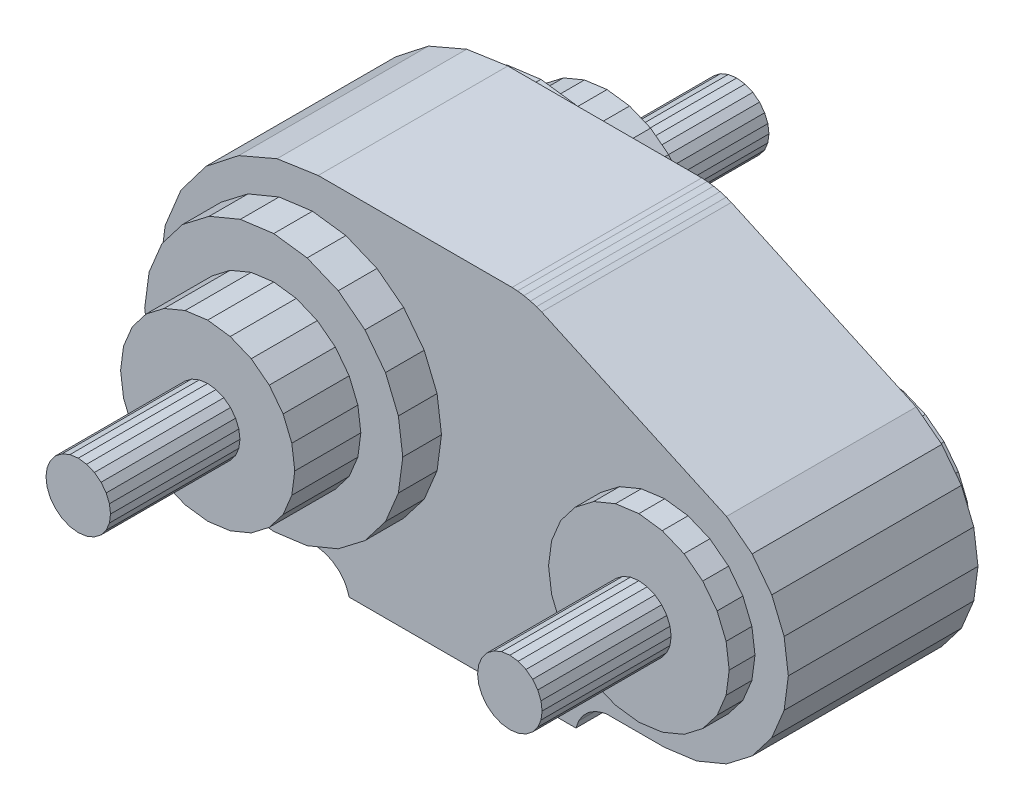
SolidWorks part; units mm, degrees
ref_plane "Front Plane" through (0, 0, 0) normal (0, 0, 1) x (1, 0, 0)
ref_plane "Top Plane" through (0, 0, 0) normal (0, 1, 0) x (1, 0, 0)
ref_plane "Right Plane" through (0, 0, 0) normal (1, 0, 0) x (0, 0, -1)
ref_plane "Plane1" through (0, 0, 14.7) normal (0, 0, 1) x (1, 0, 0)
sketch "Sketch1" plane through (0, 0, 14.7) normal (0, 0, 1) x (1, 0, 0)
  line L0 (26.9311, 2.4677) -> (29.2425, 3.4279)
  line L1 (29.2425, 3.4279) -> (31.227, 4.9532)
  line L2 (31.227, 4.9532) -> (32.7495, 6.9397)
  line L3 (32.7495, 6.9397) -> (33.7066, 9.2524)
  line L4 (33.7066, 9.2524) -> (34.033, 11.734)
  line L5 (34.033, 11.734) -> (33.7066, 14.2155)
  line L6 (33.7066, 14.2155) -> (32.7495, 16.5282)
  line L7 (32.7495, 16.5282) -> (31.227, 18.5148)
  line L8 (31.227, 18.5148) -> (29.2425, 20.04)
  line L9 (29.2425, 20.04) -> (14.9145, 26.6)
  line L10 (14.9145, 26.6) -> (14.5183, 26.7545)
  line L11 (14.5183, 26.7545) -> (14.0432, 26.8939)
  line L12 (14.0432, 26.8939) -> (13.5359, 27.0045)
  line L13 (13.5359, 27.0045) -> (13.046, 27.0755)
  line L14 (13.046, 27.0755) -> (12.6214, 27.1)
  line L15 (12.6214, 27.1) -> (-2.4029, 27.1)
  line L16 (-2.4029, 27.1) -> (-5.5929, 26.6296)
  line L17 (-5.5929, 26.6296) -> (-8.5562, 25.3579)
  line L18 (-8.5562, 25.3579) -> (-11.0949, 23.3698)
  line L19 (-11.0949, 23.3698) -> (-13.0398, 20.7978)
  line L20 (-13.0398, 20.7978) -> (-14.2612, 17.8135)
  line L21 (-14.2612, 17.8135) -> (-14.6775, 14.6159)
  line L22 (-14.6775, 14.6159) -> (-14.2612, 11.4184)
  line L23 (-14.2612, 11.4184) -> (-13.0398, 8.4341)
  line L24 (-13.0398, 8.4341) -> (-11.0949, 5.8621)
  line L25 (-11.0949, 5.8621) -> (-8.5562, 3.874)
  line L26 (-8.5562, 3.874) -> (-5.5929, 2.6023)
  line L27 (-5.5929, 2.6023) -> (-2.4029, 2.1319)
  line L28 (-2.4029, 2.1319) -> (-1.7977, 1.9932)
  line L29 (-1.7977, 1.9932) -> (-1.238, 1.7245)
  line L30 (-1.238, 1.7245) -> (-0.7514, 1.3389)
  line L31 (-0.7514, 1.3389) -> (0, 0.4064)
  line L32 (0, 0.4064) -> (0, 0)
  line L33 (0, 0) -> (17.5735, 0)
  line L34 (17.5735, 0) -> (17.5735, 0.255)
  line L35 (17.5735, 0.255) -> (18.1167, 1.108)
  line L36 (18.1167, 1.108) -> (18.5575, 1.5453)
  line L37 (18.5575, 1.5453) -> (19.0839, 1.8745)
  line L38 (19.0839, 1.8745) -> (19.8193, 2.1317)
  line L39 (19.8193, 2.1317) -> (24.45, 2.138)
  line L40 (24.45, 2.138) -> (26.9311, 2.4677)
extrude "Boss-Extrude1" add sketch "Sketch1" against normal blind 14.7
sketch "Sketch2" plane through (0, 0, 14.7) normal (0, 0, 1) x (1, 0, 0)
  line L0 (17.45, 11.83) -> (17.6885, 13.6417)
  line L1 (17.6885, 13.6417) -> (18.3878, 15.33)
  line L2 (18.3878, 15.33) -> (19.5003, 16.7797)
  line L3 (19.5003, 16.7797) -> (20.95, 17.8922)
  line L4 (20.95, 17.8922) -> (22.6383, 18.5915)
  line L5 (22.6383, 18.5915) -> (24.45, 18.83)
  line L6 (24.45, 18.83) -> (26.2617, 18.5915)
  line L7 (26.2617, 18.5915) -> (27.95, 17.8922)
  line L8 (27.95, 17.8922) -> (29.3997, 16.7797)
  line L9 (29.3997, 16.7797) -> (30.5122, 15.33)
  line L10 (30.5122, 15.33) -> (31.2115, 13.6417)
  line L11 (31.2115, 13.6417) -> (31.45, 11.83)
  line L12 (31.45, 11.83) -> (31.2115, 10.0183)
  line L13 (31.2115, 10.0183) -> (30.5122, 8.33)
  line L14 (30.5122, 8.33) -> (29.3997, 6.8803)
  line L15 (29.3997, 6.8803) -> (27.95, 5.7678)
  line L16 (27.95, 5.7678) -> (26.2617, 5.0685)
  line L17 (26.2617, 5.0685) -> (24.45, 4.83)
  line L18 (24.45, 4.83) -> (22.6383, 5.0685)
  line L19 (22.6383, 5.0685) -> (20.95, 5.7678)
  line L20 (20.95, 5.7678) -> (19.5003, 6.8803)
  line L21 (19.5003, 6.8803) -> (18.3878, 8.33)
  line L22 (18.3878, 8.33) -> (17.6885, 10.0183)
  line L23 (17.6885, 10.0183) -> (17.45, 11.83)
extrude "Boss-Extrude2" add sketch "Sketch2" along normal blind 2
sketch "Sketch3" plane through (0, 0, 16.7) normal (0, 0, 1) x (1, 0, 0)
  line L0 (21.95, 11.83) -> (22.0352, 12.477)
  line L1 (22.0352, 12.477) -> (22.2849, 13.08)
  line L2 (22.2849, 13.08) -> (22.6822, 13.5978)
  line L3 (22.6822, 13.5978) -> (23.2, 13.9951)
  line L4 (23.2, 13.9951) -> (23.803, 14.2448)
  line L5 (23.803, 14.2448) -> (24.45, 14.33)
  line L6 (24.45, 14.33) -> (25.097, 14.2448)
  line L7 (25.097, 14.2448) -> (25.7, 13.9951)
  line L8 (25.7, 13.9951) -> (26.2178, 13.5978)
  line L9 (26.2178, 13.5978) -> (26.6151, 13.08)
  line L10 (26.6151, 13.08) -> (26.8648, 12.477)
  line L11 (26.8648, 12.477) -> (26.95, 11.83)
  line L12 (26.95, 11.83) -> (26.8648, 11.183)
  line L13 (26.8648, 11.183) -> (26.6151, 10.58)
  line L14 (26.6151, 10.58) -> (26.2178, 10.0622)
  line L15 (26.2178, 10.0622) -> (25.7, 9.6649)
  line L16 (25.7, 9.6649) -> (25.097, 9.4152)
  line L17 (25.097, 9.4152) -> (24.45, 9.33)
  line L18 (24.45, 9.33) -> (23.803, 9.4152)
  line L19 (23.803, 9.4152) -> (23.2, 9.6649)
  line L20 (23.2, 9.6649) -> (22.6822, 10.0622)
  line L21 (22.6822, 10.0622) -> (22.2849, 10.58)
  line L22 (22.2849, 10.58) -> (22.0352, 11.183)
  line L23 (22.0352, 11.183) -> (21.95, 11.83)
extrude "Boss-Extrude3" add sketch "Sketch3" along normal blind 10
sketch "Sketch4" plane through (0, 0, 14.7) normal (0, 0, 1) x (1, 0, 0)
  line L0 (-0.2593, 4.8207) -> (-2.8475, 4.48)
  line L1 (-2.8475, 4.48) -> (-5.4357, 4.8207)
  line L2 (-5.4357, 4.8207) -> (-7.8475, 5.8197)
  line L3 (-7.8475, 5.8197) -> (-9.9186, 7.4089)
  line L4 (-9.9186, 7.4089) -> (-11.5078, 9.48)
  line L5 (-11.5078, 9.48) -> (-12.5068, 11.8918)
  line L6 (-12.5068, 11.8918) -> (-12.8475, 14.48)
  line L7 (-12.8475, 14.48) -> (-12.5068, 17.0682)
  line L8 (-12.5068, 17.0682) -> (-11.5078, 19.48)
  line L9 (-11.5078, 19.48) -> (-9.9186, 21.5511)
  line L10 (-9.9186, 21.5511) -> (-7.8475, 23.1403)
  line L11 (-7.8475, 23.1403) -> (-5.4357, 24.1393)
  line L12 (-5.4357, 24.1393) -> (-2.8475, 24.48)
  line L13 (-2.8475, 24.48) -> (-0.2593, 24.1393)
  line L14 (-0.2593, 24.1393) -> (2.1525, 23.1403)
  line L15 (2.1525, 23.1403) -> (4.2235, 21.5511)
  line L16 (4.2235, 21.5511) -> (5.8127, 19.48)
  line L17 (5.8127, 19.48) -> (6.8117, 17.0682)
  line L18 (6.8117, 17.0682) -> (7.1525, 14.48)
  line L19 (7.1525, 14.48) -> (6.8117, 11.8918)
  line L20 (6.8117, 11.8918) -> (5.8127, 9.48)
  line L21 (5.8127, 9.48) -> (4.2235, 7.4089)
  line L22 (4.2235, 7.4089) -> (2.1525, 5.8197)
  line L23 (2.1525, 5.8197) -> (-0.2593, 4.8207)
extrude "Boss-Extrude4" add sketch "Sketch4" along normal blind 3
sketch "Sketch5" plane through (0, 0, 17.7) normal (0, 0, 1) x (1, 0, 0)
  line L0 (-1.1005, 7.96) -> (-2.8475, 7.73)
  line L1 (-2.8475, 7.73) -> (-4.5946, 7.96)
  line L2 (-4.5946, 7.96) -> (-6.2225, 8.6343)
  line L3 (-6.2225, 8.6343) -> (-7.6205, 9.707)
  line L4 (-7.6205, 9.707) -> (-8.6932, 11.105)
  line L5 (-8.6932, 11.105) -> (-9.3675, 12.733)
  line L6 (-9.3675, 12.733) -> (-9.5975, 14.48)
  line L7 (-9.5975, 14.48) -> (-9.3675, 16.227)
  line L8 (-9.3675, 16.227) -> (-8.6932, 17.855)
  line L9 (-8.6932, 17.855) -> (-7.6205, 19.253)
  line L10 (-7.6205, 19.253) -> (-6.2225, 20.3257)
  line L11 (-6.2225, 20.3257) -> (-4.5946, 21)
  line L12 (-4.5946, 21) -> (-2.8475, 21.23)
  line L13 (-2.8475, 21.23) -> (-1.1005, 21)
  line L14 (-1.1005, 21) -> (0.5275, 20.3257)
  line L15 (0.5275, 20.3257) -> (1.9254, 19.253)
  line L16 (1.9254, 19.253) -> (2.9981, 17.855)
  line L17 (2.9981, 17.855) -> (3.6725, 16.227)
  line L18 (3.6725, 16.227) -> (3.9025, 14.48)
  line L19 (3.9025, 14.48) -> (3.6725, 12.733)
  line L20 (3.6725, 12.733) -> (2.9981, 11.105)
  line L21 (2.9981, 11.105) -> (1.9254, 9.707)
  line L22 (1.9254, 9.707) -> (0.5275, 8.6343)
  line L23 (0.5275, 8.6343) -> (-1.1005, 7.96)
extrude "Boss-Extrude5" add sketch "Sketch5" along normal blind 5.12
sketch "Sketch6" plane through (0, 0, 22.82) normal (0, 0, 1) x (1, 0, 0)
  line L0 (-1.5975, 12.3149) -> (-2.2005, 12.0652)
  line L1 (-2.2005, 12.0652) -> (-2.8475, 11.98)
  line L2 (-2.8475, 11.98) -> (-3.4946, 12.0652)
  line L3 (-3.4946, 12.0652) -> (-4.0975, 12.3149)
  line L4 (-4.0975, 12.3149) -> (-4.6153, 12.7122)
  line L5 (-4.6153, 12.7122) -> (-5.0126, 13.23)
  line L6 (-5.0126, 13.23) -> (-5.2623, 13.833)
  line L7 (-5.2623, 13.833) -> (-5.3475, 14.48)
  line L8 (-5.3475, 14.48) -> (-5.2623, 15.127)
  line L9 (-5.2623, 15.127) -> (-5.0126, 15.73)
  line L10 (-5.0126, 15.73) -> (-4.6153, 16.2478)
  line L11 (-4.6153, 16.2478) -> (-4.0975, 16.6451)
  line L12 (-4.0975, 16.6451) -> (-3.4946, 16.8948)
  line L13 (-3.4946, 16.8948) -> (-2.8475, 16.98)
  line L14 (-2.8475, 16.98) -> (-2.2005, 16.8948)
  line L15 (-2.2005, 16.8948) -> (-1.5975, 16.6451)
  line L16 (-1.5975, 16.6451) -> (-1.0798, 16.2478)
  line L17 (-1.0798, 16.2478) -> (-0.6825, 15.73)
  line L18 (-0.6825, 15.73) -> (-0.4327, 15.127)
  line L19 (-0.4327, 15.127) -> (-0.3475, 14.48)
  line L20 (-0.3475, 14.48) -> (-0.4327, 13.833)
  line L21 (-0.4327, 13.833) -> (-0.6825, 13.23)
  line L22 (-0.6825, 13.23) -> (-1.0798, 12.7122)
  line L23 (-1.0798, 12.7122) -> (-1.5975, 12.3149)
extrude "Boss-Extrude6" add sketch "Sketch6" along normal blind 10.03
sketch "Sketch7" plane through (0, 0, 0) normal (0, 0, -1) x (-1, 0, 0)
  line L0 (-27.95, 5.7678) -> (-29.3997, 6.8803)
  line L1 (-29.3997, 6.8803) -> (-30.5122, 8.33)
  line L2 (-30.5122, 8.33) -> (-31.2115, 10.0183)
  line L3 (-31.2115, 10.0183) -> (-31.45, 11.83)
  line L4 (-31.45, 11.83) -> (-31.2115, 13.6417)
  line L5 (-31.2115, 13.6417) -> (-30.5122, 15.33)
  line L6 (-30.5122, 15.33) -> (-29.3997, 16.7797)
  line L7 (-29.3997, 16.7797) -> (-27.95, 17.8922)
  line L8 (-27.95, 17.8922) -> (-26.2617, 18.5915)
  line L9 (-26.2617, 18.5915) -> (-24.45, 18.83)
  line L10 (-24.45, 18.83) -> (-22.6383, 18.5915)
  line L11 (-22.6383, 18.5915) -> (-20.95, 17.8922)
  line L12 (-20.95, 17.8922) -> (-19.5003, 16.7797)
  line L13 (-19.5003, 16.7797) -> (-18.3878, 15.33)
  line L14 (-18.3878, 15.33) -> (-17.6885, 13.6417)
  line L15 (-17.6885, 13.6417) -> (-17.45, 11.83)
  line L16 (-17.45, 11.83) -> (-17.6885, 10.0183)
  line L17 (-17.6885, 10.0183) -> (-18.3878, 8.33)
  line L18 (-18.3878, 8.33) -> (-19.5003, 6.8803)
  line L19 (-19.5003, 6.8803) -> (-20.95, 5.7678)
  line L20 (-20.95, 5.7678) -> (-22.6383, 5.0685)
  line L21 (-22.6383, 5.0685) -> (-24.45, 4.83)
  line L22 (-24.45, 4.83) -> (-26.2617, 5.0685)
  line L23 (-26.2617, 5.0685) -> (-27.95, 5.7678)
extrude "Boss-Extrude7" add sketch "Sketch7" along normal blind 2
sketch "Sketch8" plane through (0, 0, 0) normal (0, 0, -1) x (-1, 0, 0)
  line L0 (9.9186, 21.5511) -> (11.5078, 19.48)
  line L1 (11.5078, 19.48) -> (12.5068, 17.0682)
  line L2 (12.5068, 17.0682) -> (12.8475, 14.48)
  line L3 (12.8475, 14.48) -> (12.5068, 11.8918)
  line L4 (12.5068, 11.8918) -> (11.5078, 9.48)
  line L5 (11.5078, 9.48) -> (9.9186, 7.4089)
  line L6 (9.9186, 7.4089) -> (7.8475, 5.8197)
  line L7 (7.8475, 5.8197) -> (5.4357, 4.8207)
  line L8 (5.4357, 4.8207) -> (2.8475, 4.48)
  line L9 (2.8475, 4.48) -> (0.2593, 4.8207)
  line L10 (0.2593, 4.8207) -> (-2.1525, 5.8197)
  line L11 (-2.1525, 5.8197) -> (-4.2235, 7.4089)
  line L12 (-4.2235, 7.4089) -> (-5.8127, 9.48)
  line L13 (-5.8127, 9.48) -> (-6.8117, 11.8918)
  line L14 (-6.8117, 11.8918) -> (-7.1525, 14.48)
  line L15 (-7.1525, 14.48) -> (-6.8117, 17.0682)
  line L16 (-6.8117, 17.0682) -> (-5.8127, 19.48)
  line L17 (-5.8127, 19.48) -> (-4.2235, 21.5511)
  line L18 (-4.2235, 21.5511) -> (-2.1525, 23.1403)
  line L19 (-2.1525, 23.1403) -> (0.2593, 24.1393)
  line L20 (0.2593, 24.1393) -> (2.8475, 24.48)
  line L21 (2.8475, 24.48) -> (5.4357, 24.1393)
  line L22 (5.4357, 24.1393) -> (7.8475, 23.1403)
  line L23 (7.8475, 23.1403) -> (9.9186, 21.5511)
extrude "Boss-Extrude8" add sketch "Sketch8" along normal blind 3
sketch "Sketch9" plane through (0, 0, -3) normal (0, 0, -1) x (-1, 0, 0)
  line L0 (4.5946, 21) -> (6.2225, 20.3257)
  line L1 (6.2225, 20.3257) -> (7.6205, 19.253)
  line L2 (7.6205, 19.253) -> (8.6932, 17.855)
  line L3 (8.6932, 17.855) -> (9.3675, 16.227)
  line L4 (9.3675, 16.227) -> (9.5975, 14.48)
  line L5 (9.5975, 14.48) -> (9.3675, 12.733)
  line L6 (9.3675, 12.733) -> (8.6932, 11.105)
  line L7 (8.6932, 11.105) -> (7.6205, 9.707)
  line L8 (7.6205, 9.707) -> (6.2225, 8.6343)
  line L9 (6.2225, 8.6343) -> (4.5946, 7.96)
  line L10 (4.5946, 7.96) -> (2.8475, 7.73)
  line L11 (2.8475, 7.73) -> (1.1005, 7.96)
  line L12 (1.1005, 7.96) -> (-0.5275, 8.6343)
  line L13 (-0.5275, 8.6343) -> (-1.9254, 9.707)
  line L14 (-1.9254, 9.707) -> (-2.9981, 11.105)
  line L15 (-2.9981, 11.105) -> (-3.6725, 12.733)
  line L16 (-3.6725, 12.733) -> (-3.9025, 14.48)
  line L17 (-3.9025, 14.48) -> (-3.6725, 16.227)
  line L18 (-3.6725, 16.227) -> (-2.9981, 17.855)
  line L19 (-2.9981, 17.855) -> (-1.9254, 19.253)
  line L20 (-1.9254, 19.253) -> (-0.5275, 20.3257)
  line L21 (-0.5275, 20.3257) -> (1.1005, 21)
  line L22 (1.1005, 21) -> (2.8475, 21.23)
  line L23 (2.8475, 21.23) -> (4.5946, 21)
extrude "Boss-Extrude9" add sketch "Sketch9" along normal blind 5.13
sketch "Sketch10" plane through (0, 0, -8.13) normal (0, 0, -1) x (-1, 0, 0)
  line L0 (0.4327, 13.833) -> (0.3475, 14.48)
  line L1 (0.3475, 14.48) -> (0.4327, 15.127)
  line L2 (0.4327, 15.127) -> (0.6825, 15.73)
  line L3 (0.6825, 15.73) -> (1.0798, 16.2478)
  line L4 (1.0798, 16.2478) -> (1.5975, 16.6451)
  line L5 (1.5975, 16.6451) -> (2.2005, 16.8948)
  line L6 (2.2005, 16.8948) -> (2.8475, 16.98)
  line L7 (2.8475, 16.98) -> (3.4946, 16.8948)
  line L8 (3.4946, 16.8948) -> (4.0975, 16.6451)
  line L9 (4.0975, 16.6451) -> (4.6153, 16.2478)
  line L10 (4.6153, 16.2478) -> (5.0126, 15.73)
  line L11 (5.0126, 15.73) -> (5.2623, 15.127)
  line L12 (5.2623, 15.127) -> (5.3475, 14.48)
  line L13 (5.3475, 14.48) -> (5.2623, 13.833)
  line L14 (5.2623, 13.833) -> (5.0126, 13.23)
  line L15 (5.0126, 13.23) -> (4.6153, 12.7122)
  line L16 (4.6153, 12.7122) -> (4.0975, 12.3149)
  line L17 (4.0975, 12.3149) -> (3.4946, 12.0652)
  line L18 (3.4946, 12.0652) -> (2.8475, 11.98)
  line L19 (2.8475, 11.98) -> (2.2005, 12.0652)
  line L20 (2.2005, 12.0652) -> (1.5975, 12.3149)
  line L21 (1.5975, 12.3149) -> (1.0798, 12.7122)
  line L22 (1.0798, 12.7122) -> (0.6825, 13.23)
  line L23 (0.6825, 13.23) -> (0.4327, 13.833)
extrude "Boss-Extrude10" add sketch "Sketch10" along normal blind 10.05
sketch "Sketch11" plane through (0, 0, 0) normal (0, -1, 0) x (1, 0, 0)
  line L0 (13.479, 2.8434) -> (13.809, 2.8)
  line L1 (13.809, 2.8) -> (14.139, 2.8434)
  line L2 (14.139, 2.8434) -> (14.4465, 2.9708)
  line L3 (14.4465, 2.9708) -> (14.7105, 3.1734)
  line L4 (14.7105, 3.1734) -> (14.9132, 3.4375)
  line L5 (14.9132, 3.4375) -> (15.0405, 3.745)
  line L6 (15.0405, 3.745) -> (15.084, 4.075)
  line L7 (15.084, 4.075) -> (15.0405, 4.405)
  line L8 (15.0405, 4.405) -> (14.9132, 4.7125)
  line L9 (14.9132, 4.7125) -> (14.7105, 4.9766)
  line L10 (14.7105, 4.9766) -> (14.4465, 5.1792)
  line L11 (14.4465, 5.1792) -> (14.139, 5.3066)
  line L12 (14.139, 5.3066) -> (13.809, 5.35)
  line L13 (13.809, 5.35) -> (13.479, 5.3066)
  line L14 (13.479, 5.3066) -> (13.1715, 5.1792)
  line L15 (13.1715, 5.1792) -> (12.9074, 4.9766)
  line L16 (12.9074, 4.9766) -> (12.7048, 4.7125)
  line L17 (12.7048, 4.7125) -> (12.5774, 4.405)
  line L18 (12.5774, 4.405) -> (12.534, 4.075)
  line L19 (12.534, 4.075) -> (12.5774, 3.745)
  line L20 (12.5774, 3.745) -> (12.7048, 3.4375)
  line L21 (12.7048, 3.4375) -> (12.9074, 3.1734)
  line L22 (12.9074, 3.1734) -> (13.1715, 2.9708)
  line L23 (13.1715, 2.9708) -> (13.479, 2.8434)
extrude "Cut-Extrude1" cut sketch "Sketch11" against normal blind 6
sketch "Sketch12" plane through (0, 0, 0) normal (0, -1, 0) x (1, 0, 0)
  line L0 (2.5774, 3.745) -> (2.7048, 3.4375)
  line L1 (2.7048, 3.4375) -> (2.9074, 3.1734)
  line L2 (2.9074, 3.1734) -> (3.1715, 2.9708)
  line L3 (3.1715, 2.9708) -> (3.479, 2.8434)
  line L4 (3.479, 2.8434) -> (3.809, 2.8)
  line L5 (3.809, 2.8) -> (4.139, 2.8434)
  line L6 (4.139, 2.8434) -> (4.4465, 2.9708)
  line L7 (4.4465, 2.9708) -> (4.7105, 3.1734)
  line L8 (4.7105, 3.1734) -> (4.9132, 3.4375)
  line L9 (4.9132, 3.4375) -> (5.0405, 3.745)
  line L10 (5.0405, 3.745) -> (5.084, 4.075)
  line L11 (5.084, 4.075) -> (5.0405, 4.405)
  line L12 (5.0405, 4.405) -> (4.9132, 4.7125)
  line L13 (4.9132, 4.7125) -> (4.7105, 4.9766)
  line L14 (4.7105, 4.9766) -> (4.4465, 5.1792)
  line L15 (4.4465, 5.1792) -> (4.139, 5.3066)
  line L16 (4.139, 5.3066) -> (3.809, 5.35)
  line L17 (3.809, 5.35) -> (3.479, 5.3066)
  line L18 (3.479, 5.3066) -> (3.1715, 5.1792)
  line L19 (3.1715, 5.1792) -> (2.9074, 4.9766)
  line L20 (2.9074, 4.9766) -> (2.7048, 4.7125)
  line L21 (2.7048, 4.7125) -> (2.5774, 4.405)
  line L22 (2.5774, 4.405) -> (2.534, 4.075)
  line L23 (2.534, 4.075) -> (2.5774, 3.745)
extrude "Cut-Extrude2" cut sketch "Sketch12" against normal blind 6
draft "Draft1" type of draft neutral plane draft angle 19.743 faces to draft 2 face at (0, 0.2032, 7.35) face at (17.5735, 0.1275, 7.35) neutral plane through (0, 0, 0) neutral plane normal (0, -1, 0) parameters "D1"=19.743
chamfer "Chamfer1" distance 0.157 angle 9.638 1 edges at (19.8193, 2.1317, 7.35)
chamfer "Chamfer2" distance 0.1576 angle 9.559 1 edges at (-0.263, 0.7327, 7.35)
